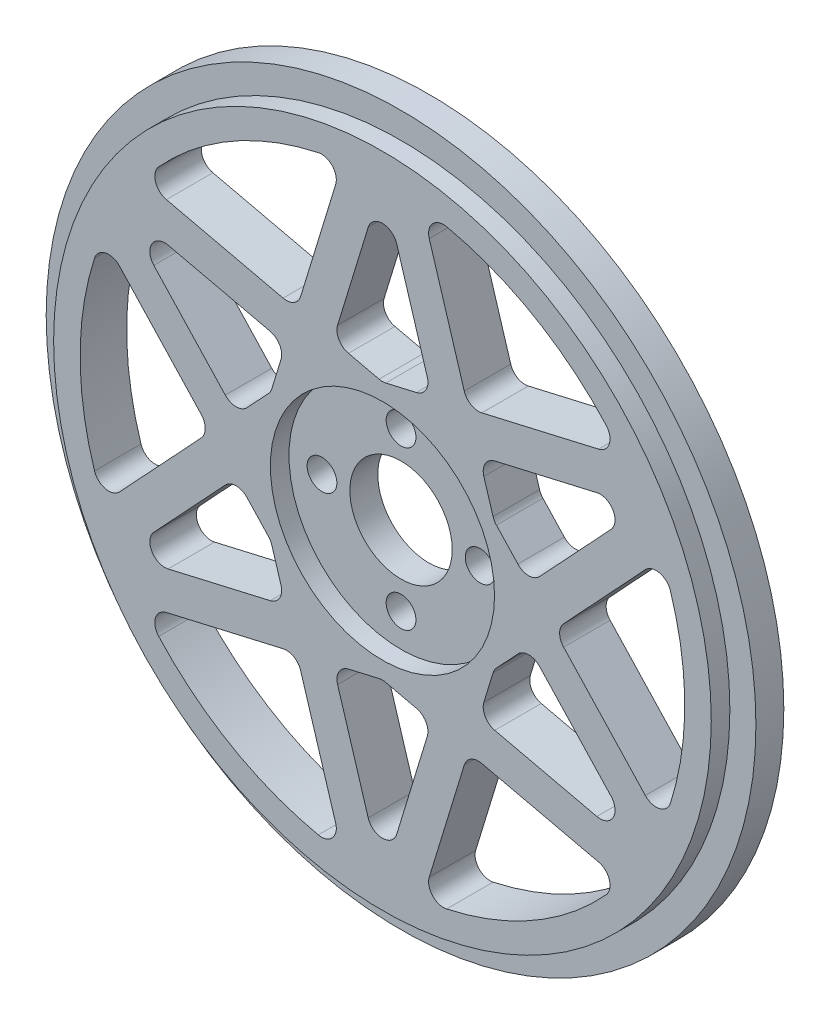
SolidWorks part; units mm, degrees
material "2018 合金"
ref_plane "正面" through (0, 0, 0) normal (0, 0, 1) x (1, 0, 0)
ref_plane "平面" through (0, 0, 0) normal (0, 1, 0) x (1, 0, 0)
ref_plane "右側面" through (0, 0, 0) normal (1, 0, 0) x (0, 0, -1)
sketch "ｽｹｯﾁ1" plane through (0, 0, 0) normal (0, 0, 1) x (1, 0, 0)
  circle A0 centre (0, 0) radius 38.15
  dimension "D1" = 76.3
extrude "ﾎﾞｽ - 押し出し1" add sketch "ｽｹｯﾁ1" along normal blind 3
sketch "ｽｹｯﾁ2" plane through (0, 0, 3) normal (0, 0, 1) x (1, 0, 0)
  circle A0 centre (0, 0) radius 35.35
  circle A1 centre (0, 0) radius 38.15 construction
  dimension "D1" = 2.8
extrude "ﾎﾞｽ - 押し出し2" add sketch "ｽｹｯﾁ2" along normal blind 2
sketch "ｽｹｯﾁ6" plane through (0, 0, 5) normal (0, 0, 1) x (1, 0, 0)
  circle A0 centre (0, 0) radius 5.5
  dimension "D1" = 11
extrude "ｶｯﾄ - 押し出し2" cut sketch "ｽｹｯﾁ6" against normal through all
sketch "ｽｹｯﾁ7" plane through (0, 0, 5) normal (0, 0, 1) x (1, 0, 0)
  circle A0 centre (0, 0) radius 13.5
  circle A1 centre (0, 0) radius 32.5
  circle A2 centre (0, 0) radius 5.5 construction
  dimension "D1" = 65
  dimension "D2" = 8
extrude "ｶｯﾄ - 押し出し3" cut sketch "ｽｹｯﾁ7" against normal through all and the other way through all
sketch "ｽｹｯﾁ8" plane through (0, 0, 5) normal (0, 0, 1) x (1, 0, 0)
  line L0 (-12.9104, 3.9462) -> (-4.2687, 32.2184)
  line L1 (0, 32.5) -> (-6.2814, 11.9497)
  line L2 (0, 0) -> (0, 32.5) construction
  circle A0 centre (0, 0) radius 13.5 construction
  circle A1 centre (0, 0) radius 32.5 construction
  arc A2 (0, 32.5) -> (-4.2687, 32.2184) centre (0, 0) ccw
  arc A3 (-6.2814, 11.9497) -> (-12.9104, 3.9462) centre (0, 0) ccw
  dimension "D1" = 4
extrude "ﾎﾞｽ - 押し出し4" add sketch "ｽｹｯﾁ8" against normal up to surface (5 mm away) up to face at (5.5, 0, 0)
pattern_circular "円形ﾊﾟﾀｰﾝ3" count 6 over 360 about axis through (0, 0, 0) along (0, 0, 1) of "ﾎﾞｽ - 押し出し4"
mirror "ﾐﾗｰ1" about plane through (0, 0, 0) normal (1, 0, 0) of "円形ﾊﾟﾀｰﾝ3", "ﾎﾞｽ - 押し出し4"
sketch "ｽｹｯﾁ9" plane through (0, 0, 5) normal (0, 0, 1) x (1, 0, 0)
  circle A0 centre (0, 0) radius 8.5 construction
  circle A1 centre (-8.5, 0) radius 1.6
  circle A2 centre (0, 8.5) radius 1.6
  circle A3 centre (8.5, 0) radius 1.6
  circle A4 centre (0, -8.5) radius 1.6
  dimension "D1" = 17
  dimension "D2" = 3.2
extrude "ｶｯﾄ - 押し出し4" cut sketch "ｽｹｯﾁ9" against normal through all
fillet "ﾌｨﾚｯﾄ3" radius 1.6 24 edges at (4.2687, -32.2184, 2.5) (25.7676, -19.8061, 2.5) (9.23, -15.9869, 2.5) (28.1458, -16.25, 2.5) (10.4021, -12.1523, 2.5) (11.9991, -6.9277, 2.5) (15.7252, -2.9323, 2.5) (30.0364, -12.4124, 2.5) (30.0364, 12.4124, 2.5) (18.4601, 0, 2.5) (15.7252, 2.9323, 2.5) (28.1458, 16.25, 2.5) (11.9991, 6.9277, 2.5) (10.4021, 12.1523, 2.5) (4.2687, 32.2184, 2.5) (25.7676, 19.8061, 2.5) (9.23, 15.9869, 2.5) (5.3231, 15.0846, 2.5) (0, 13.8553, 2.5) (0, 32.5, 2.5) (-5.3231, 15.0846, 2.5) (-25.7676, 19.8061, 2.5) (-9.23, 15.9869, 2.5) (-4.2687, 32.2184, 2.5)
fillet "ﾌｨﾚｯﾄ4" radius 1.6 18 edges at (-28.1458, 16.25, 2.5) (-10.4021, 12.1523, 2.5) (-11.9991, 6.9277, 2.5) (-15.7252, 2.9323, 2.5) (-30.0364, -12.4124, 2.5) (-30.0364, 12.4124, 2.5) (-18.4601, 0, 2.5) (-28.1458, -16.25, 2.5) (-15.7252, -2.9323, 2.5) (-11.9991, -6.9277, 2.5) (-10.4021, -12.1523, 2.5) (-25.7676, -19.8061, 2.5) (-9.23, -15.9869, 2.5) (-4.2687, -32.2184, 2.5) (0, -32.5, 2.5) (-5.3231, -15.0846, 2.5) (0, -13.8553, 2.5) (5.3231, -15.0846, 2.5)
sketch "ｽｹｯﾁ11" plane through (0, 0, 5) normal (0, 0, 1) x (1, 0, 0)
  circle A0 centre (0, 0) radius 12.05
  dimension "D1" = 24.1
extrude "ｶｯﾄ - 押し出し6" cut sketch "ｽｹｯﾁ11" against normal blind 2
